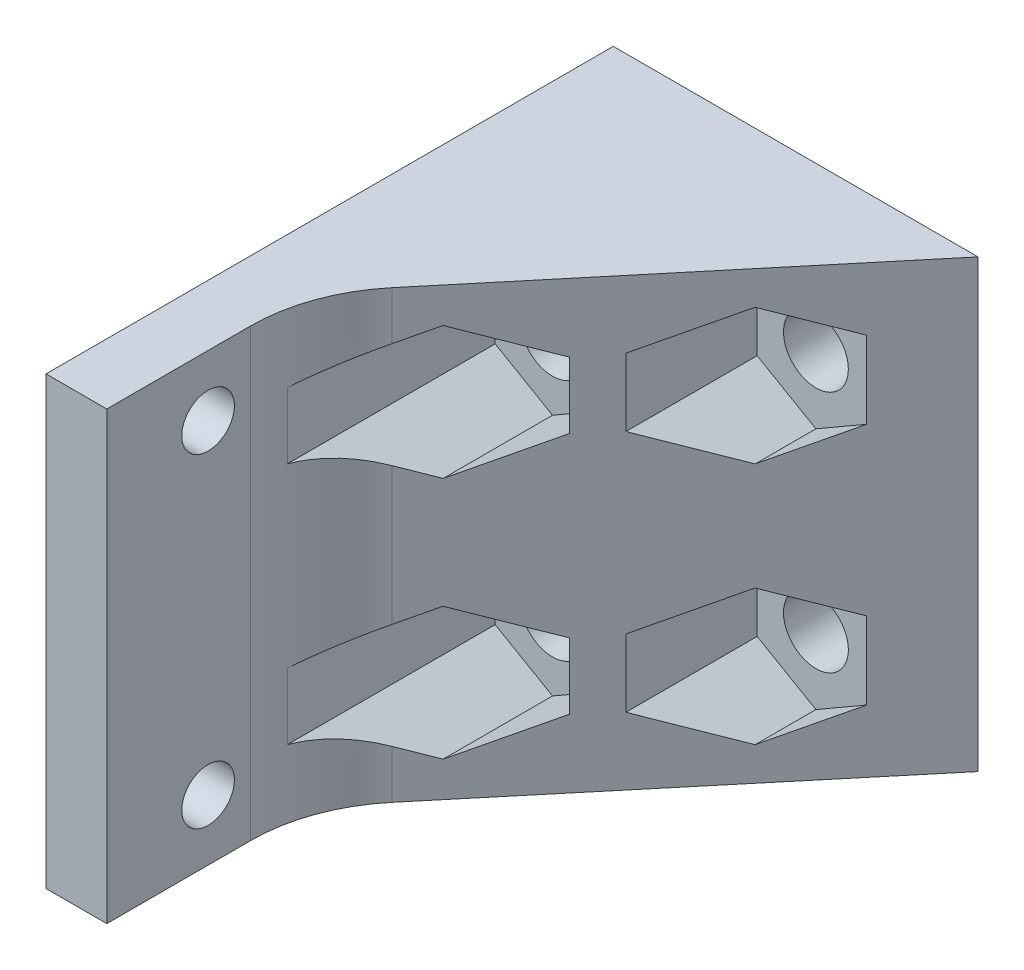
SolidWorks part; units mm, degrees
ref_plane "Front Plane" through (0, 0, 0) normal (0, 0, 1) x (1, 0, 0)
ref_plane "Top Plane" through (0, 0, 0) normal (0, 1, 0) x (1, 0, 0)
ref_plane "Right Plane" through (0, 0, 0) normal (1, 0, 0) x (0, 0, -1)
sketch "Sketch1" plane through (0, 0, 0) normal (1, 0, 0) x (0, 0, -1)
  line L0 (0, 11) -> (28, 11) construction
  line L1 (0, 0) -> (28, 0)
  line L2 (0, 0) -> (0, 22)
  line L3 (0, 22) -> (28, 22)
  line L4 (28, 0) -> (28, 22)
  circle A0 centre (5, 19) radius 1.3
  circle A1 centre (5, 3) radius 1.3
  dimension "D3" = 2.6
  dimension "D4" = 23
  dimension "D5" = 8
  dimension "D1" = 22
  dimension "D2" = 28
extrude "Boss-Extrude1" add sketch "Sketch1" along normal blind 3 contours L2 L3 L4 L1
sketch "Sketch3" plane through (0, 0, 0) normal (0, 1, 0) x (1, 0, 0)
  line L0 (3, 28) -> (18, 28)
  line L1 (18, 28) -> (3, 10)
  line L2 (3, 28) -> (3, 0) construction
  line L3 (3, 28) -> (3, 10)
  dimension "D1" = 18
  dimension "D2" = 15
extrude "Boss-Extrude3" add sketch "Sketch3" along normal up to surface (22 mm away) contours L1 L3 L0 up to face at (1.5, 22, -14)
fillet "Fillet1" radius 8 1 edges at (3, 11, -10)
sketch "Sketch4" plane through (0, 0, -28) normal (0, 0, -1) x (-1, 0, 0)
  line L0 (-9, 0) -> (-9, 22) construction
  line L1 (-18, 0) -> (0, 0) construction
  line L2 (-18, 22) -> (0, 22) construction
  line L3 (-18, 11) -> (0, 11) construction
  line L4 (-18, 22) -> (-18, 0) construction
  line L5 (0, 0) -> (0, 22) construction
  line L6 (-25, 11) -> (-7, 11) construction
  circle A1 centre (-6, 17) radius 1.6
  circle A2 centre (-6, 5) radius 1.6
  circle A4 centre (-13, 17) radius 1.6
  circle A5 centre (-13, 5) radius 1.6
  dimension "D1" = 3.2
  dimension "D2" = 3
  dimension "D3" = 6
  dimension "D4" = 2
extrude "Cut-Extrude1" cut sketch "Sketch4" against normal through all
ref_plane "Plane1" through (0, 0, -19) normal (0, 0, 1) x (1, 0, 0)
ref_plane "Plane2" through (0, 0, -25) normal (0, 0, 1) x (1, 0, 0)
sketch "Sketch5" plane through (0, 0, -19) normal (0, 0, 1) x (1, 0, 0)
  line L0 (18, 11) -> (0, 11) construction
  line L7 (18, 22) -> (18, 0) construction
  line L8 (0, 22) -> (0, 0) construction
  line L15 (3.1695, 3.3658) -> (3.1695, 6.6342)
  line L16 (3.1695, 15.3658) -> (6, 13.7316)
  line L17 (6, 13.7316) -> (8.8305, 15.3658)
  line L18 (8.8305, 15.3658) -> (8.8305, 18.6342)
  line L19 (8.8305, 18.6342) -> (6, 20.2684)
  line L20 (6, 20.2684) -> (3.1695, 18.6342)
  line L21 (3.1695, 18.6342) -> (3.1695, 15.3658)
  line L22 (6, 1.7316) -> (3.1695, 3.3658)
  line L23 (8.8305, 3.3658) -> (6, 1.7316)
  line L24 (8.8305, 6.6342) -> (8.8305, 3.3658)
  line L25 (6, 8.2684) -> (8.8305, 6.6342)
  line L26 (3.1695, 6.6342) -> (6, 8.2684)
  circle A0 centre (6, 5) radius 2.8305 construction
  circle A1 centre (6, 17) radius 2.8305 construction
  point P21 (3.1695, 17)
  dimension "D2" = 5.661
  dimension "D3" = 0
extrude "Cut-Extrude2" cut sketch "Sketch5" along normal through all
sketch "Sketch6" plane through (0, 0, -25) normal (0, 0, 1) x (1, 0, 0)
  line L0 (18, 11) -> (0, 11) construction
  line L7 (18, 22) -> (18, 0) construction
  line L8 (0, 22) -> (0, 0) construction
  line L16 (10.1, 15.3257) -> (13, 13.6514)
  line L17 (13, 13.6514) -> (15.9, 15.3257)
  line L18 (15.9, 15.3257) -> (15.9, 18.6743)
  line L19 (15.9, 18.6743) -> (13, 20.3486)
  line L20 (13, 20.3486) -> (10.1, 18.6743)
  line L21 (10.1, 18.6743) -> (10.1, 15.3257)
  line L22 (4.8542, 22) -> (18, 22) construction
  line L23 (10.1, 3.3257) -> (10.1, 6.6743)
  line L24 (13, 1.6514) -> (10.1, 3.3257)
  line L25 (15.9, 3.3257) -> (13, 1.6514)
  line L26 (15.9, 6.6743) -> (15.9, 3.3257)
  line L27 (13, 8.3486) -> (15.9, 6.6743)
  line L28 (10.1, 6.6743) -> (13, 8.3486)
  circle A0 centre (13, 5) radius 2.9 construction
  circle A1 centre (13, 17) radius 2.9 construction
  circle A2 centre (13, 17) radius 1.6 construction
  dimension "D3" = 1.3
  dimension "D1" = 90
  dimension "D2" = 5.8
extrude "Cut-Extrude3" cut sketch "Sketch6" along normal through all
